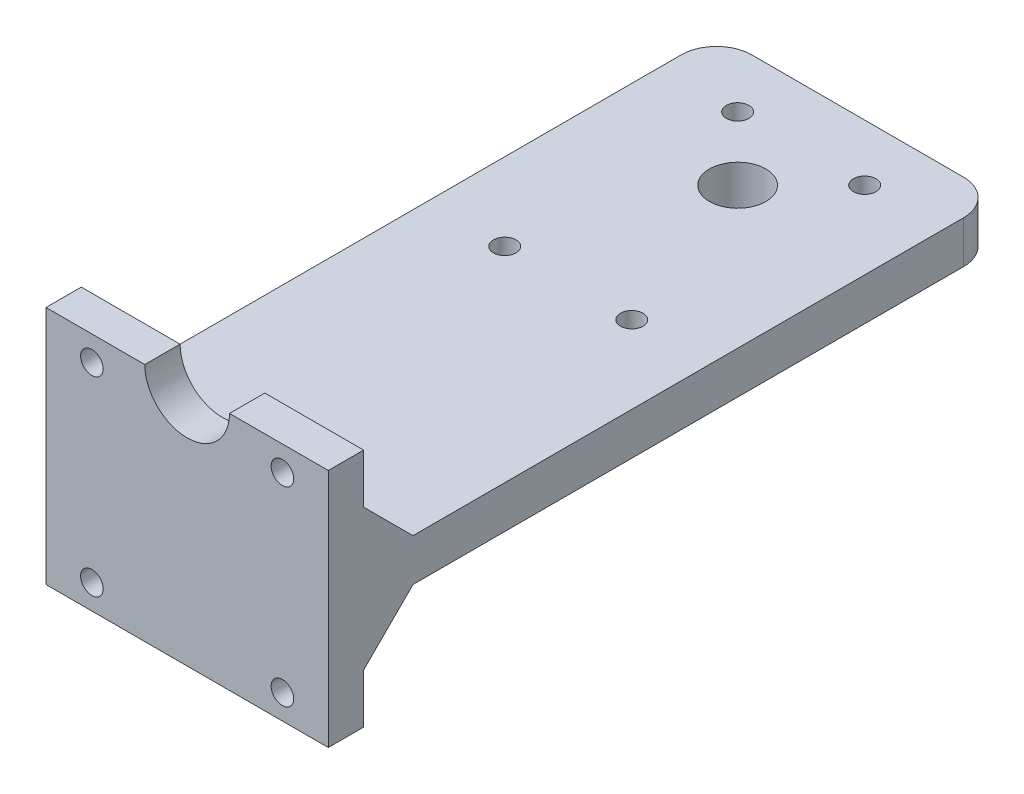
SolidWorks part; units mm, degrees
material "PET"
ref_plane "Спереди" through (0, 0, 0) normal (0, 0, 1) x (1, 0, 0)
ref_plane "Сверху" through (0, 0, 0) normal (0, 1, 0) x (1, 0, 0)
ref_plane "Справа" through (0, 0, 0) normal (1, 0, 0) x (0, 0, -1)
sketch "Эскиз1" plane through (0, 0, 0) normal (0, 1, 0) x (1, 0, 0)
  line L0 (0, 47.5) -> (0, 110.9889) construction
  line L1 (20, 95) -> (-20, 95)
  line L2 (20, 95) -> (20, 0)
  line L3 (20, 0) -> (-20, 0)
  line L4 (-20, 95) -> (-20, 0)
  line L5 (20, 95) -> (-20, 0) construction
  line L6 (20, 0) -> (-20, 95) construction
  circle A0 centre (0, 78) radius 4
  circle A1 centre (-9, 87) radius 1.6
  circle A2 centre (9, 87) radius 1.6
  circle A3 centre (-9, 54) radius 1.6
  circle A4 centre (9, 54) radius 1.6
  point P0 (0, 47.5)
  point P5 (0, 0)
  dimension "D3" = 8
  dimension "D4" = 78
  dimension "D7" = 3.2
  dimension "D10" = 3.2
  dimension "D1" = 95
  dimension "D2" = 40
  dimension "D5" = 9
  dimension "D6" = 18
  dimension "D8" = 18
  dimension "D9" = 33
extrude "Бобышка-Вытянуть1" add sketch "Эскиз1" along normal blind 6
sketch "Эскиз2" plane through (0, 6, 0) normal (0, 1, 0) x (1, 0, 0)
  line L0 (20, 0) -> (20, 95) construction
  line L1 (-20, 0) -> (20, 0)
  line L2 (-20, 0) -> (-20, 5)
  line L3 (-20, 5) -> (20, 5)
  line L4 (20, 0) -> (20, 5)
  dimension "D1" = 5
extrude "Бобышка-Вытянуть2" add sketch "Эскиз2" along normal blind 14
sketch "Эскиз3" plane through (0, 0, -5) normal (0, 0, -1) x (-1, 0, 0)
  line L0 (-20, 20) -> (20, 20) construction
  circle A0 centre (0, 20) radius 6
  dimension "D1" = 12
extrude "Вырез-Вытянуть1" cut sketch "Эскиз3" against normal blind 14
chamfer "Фаска1" distance 7 angle 45 1 edges at (0, 6, -5)
sketch "Эскиз4" plane through (0, 0, -5) normal (0, 0, -1) x (-1, 0, 0)
  line L0 (0, 19.8869) -> (0, -3.1679) construction
  line L1 (-20, 20) -> (-6, 20) construction
  circle A0 centre (13.5, 16.5) radius 1.6
  circle A1 centre (-13.5, 16.5) radius 1.6
  dimension "D1" = 3.2
  dimension "D2" = 3.5
  dimension "D3" = 27
extrude "Вырез-Вытянуть2" cut sketch "Эскиз4" against normal blind 14
fillet "Скругление1" radius 5 2 edges at (20, 3, -95) (-20, 3, -95)
sketch "Эскиз5" plane through (20, 0, 0) normal (1, 0, 0) x (0, 0, -1)
  line L5 (5, -7) -> (5, -14)
  line L6 (5, -14) -> (0, -14)
  line L21 (0, -14) -> (0, 0)
  line L22 (12, 0) -> (0, 0)
  line L23 (12, 0) -> (5, -7)
extrude "Бобышка-Вытянуть3" add sketch "Эскиз5" against normal blind 40
sketch "Эскиз6" plane through (-20, 0, 0) normal (-1, 0, 0) x (0, 0, 1)
  line L0 (0, 3) -> (-25.7918, 3) construction
  line L1 (0, 20) -> (0, -14) construction
sketch "Эскиз7" plane through (0, 0, 0) normal (0, 0, 1) x (1, 0, 0)
  line L0 (-20, 3) -> (20.7176, 3) construction
  line L1 (-20, 20) -> (-20, -14) construction
  circle A0 centre (13.5, 16.5) radius 1.6 construction
  circle A1 centre (-13.5, 16.5) radius 1.6 construction
  circle A4 centre (13.5, -10.5) radius 1.6
  circle A5 centre (-13.5, -10.5) radius 1.6
extrude "Вырез-Вытянуть3" cut sketch "Эскиз7" against normal blind 40
sketch "Эскиз8" plane through (0, 0, 0) normal (0, 0, 1) x (1, 0, 0)
  circle A0 centre (13.5, 16.5) radius 1.553
  circle A1 centre (13.5, -10.5) radius 1.6
